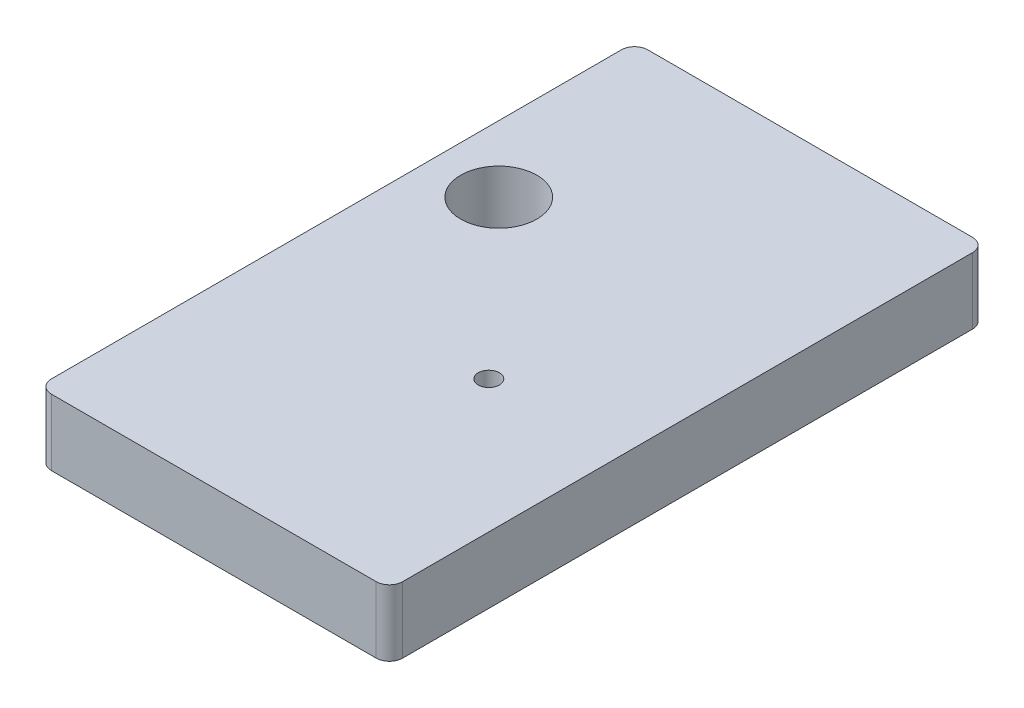
SolidWorks part; units mm, degrees
ref_plane "Plan de face" through (0, 0, 0) normal (0, 0, 1) x (1, 0, 0)
ref_plane "Plan de dessus" through (0, 0, 0) normal (0, 1, 0) x (1, 0, 0)
ref_plane "Plan de droite" through (0, 0, 0) normal (1, 0, 0) x (0, 0, -1)
sketch "Esquisse1" plane through (0, 0, 0) normal (0, 1, 0) x (1, 0, 0)
  line L0 (-6.427, 0) -> (109.1376, 0) construction
  line L1 (0, -7.0221) -> (0, 103.9034) construction
  line L2 (53, -7.0221) -> (53, 103.9034) construction
  line L3 (-6.427, 40) -> (85.7278, 40) construction
  line L4 (-6.427, 90) -> (109.1376, 90) construction
  line L5 (-6.427, 59.5) -> (31.5612, 59.5) construction
  line L6 (0, 88) -> (0, 2)
  line L7 (2, 0) -> (51, 0)
  line L8 (53, 88) -> (53, 2)
  line L9 (10, 81.6582) -> (10, 48.1074) construction
  line L10 (13, 103.9034) -> (13, -7.0221) construction
  line L11 (2, 90) -> (51, 90)
  line L12 (33, 66.665) -> (33, 23.6354) construction
  line L13 (48.8784, 35) -> (28.9431, 35) construction
  arc A0 (51, 90) -> (53, 88) centre (51, 88) cw
  arc A1 (2, 90) -> (0, 88) centre (2, 88) ccw
  arc A2 (51, 0) -> (53, 2) centre (51, 2) ccw
  arc A3 (0, 2) -> (2, 0) centre (2, 2) ccw
  circle A4 centre (10, 59.5) radius 5.75
  circle A5 centre (33, 35) radius 1.6
  point P12 (53, 90)
  point P19 (0, 90)
  point P26 (0, 0)
  dimension "D3" = 2
  dimension "D7" = 10
  dimension "D5" = 2
  dimension "D8" = 5
  dimension "D1" = 90
  dimension "D2" = 40
  dimension "D4" = 50
  dimension "D6" = 19.5
  dimension "D9" = 20
extrude "Extrusion1" add sketch "Esquisse1" along normal blind 10
sketch "Esquisse2" plane through (0, 0, 0) normal (0, -1, 0) x (1, 0, 0)
  line L0 (57.4636, -79) -> (-27.3834, -79) construction
  line L1 (-17.6242, -59.5) -> (57.4636, -59.5) construction
  line L2 (57.4636, -40) -> (-27.3834, -40) construction
  line L3 (57.4636, -20) -> (-27.3834, -20) construction
  line L4 (53, -103.2829) -> (53, 4.7947) construction
  line L5 (57.4636, -10) -> (-27.3834, -10) construction
  line L6 (48, -121.675) -> (48, 4.7947) construction
  line L7 (42, -111.2442) -> (42, 4.7947) construction
  line L8 (57.4636, -90) -> (-27.3834, -90) construction
  line L9 (57.4636, -85) -> (-27.3834, -85) construction
  line L10 (33, -121.675) -> (33, -69.6956) construction
  line L11 (41, -103.2829) -> (41, -69.6956) construction
  line L12 (57.4636, -49.5) -> (28.6431, -49.5) construction
  line L13 (37.3159, -82) -> (19.2671, -82) construction
  line L14 (45, -57.6837) -> (45, -3.061) construction
  line L15 (42, -49.5) -> (49.9748, -57.4748) construction
  line L16 (41, -82.7373) -> (41, -81.2627)
  line L17 (41, -85) -> (33.7489, -77.7489) construction
  line L18 (45.7373, -49.5) -> (44.2627, -49.5)
  line L19 (45.7373, -69.5) -> (44.2627, -69.5)
  line L20 (25, -82.7373) -> (25, -81.2627)
  line L21 (38.7373, -85) -> (27.2627, -85)
  line L22 (38.7373, -79) -> (27.2627, -79)
  line L23 (48, -67.2373) -> (48, -51.7627)
  line L24 (42, -67.2373) -> (42, -51.7627)
  line L25 (24, -67.2373) -> (24, -51.7627)
  line L26 (18, -67.2373) -> (18, -51.7627)
  line L27 (20.2627, -69.5) -> (21.7373, -69.5)
  line L28 (20.2627, -49.5) -> (21.7373, -49.5)
  line L29 (57.4636, -7) -> (6.2084, -7) construction
  line L30 (57.4636, -23) -> (6.2084, -23) construction
  arc A0 (44.2627, -49.5) -> (42, -51.7627) centre (43.1314, -50.6314) ccw
  arc A1 (38.7373, -85) -> (41, -82.7373) centre (39.8686, -83.8686) ccw
  arc A2 (38.7373, -79) -> (41, -81.2627) centre (39.8686, -80.1314) cw
  arc A3 (27.2627, -85) -> (25, -82.7373) centre (26.1314, -83.8686) cw
  arc A4 (27.2627, -79) -> (25, -81.2627) centre (26.1314, -80.1314) ccw
  arc A5 (45.7373, -49.5) -> (48, -51.7627) centre (46.8686, -50.6314) cw
  arc A6 (44.2627, -69.5) -> (42, -67.2373) centre (43.1314, -68.3686) cw
  arc A7 (45.7373, -69.5) -> (48, -67.2373) centre (46.8686, -68.3686) ccw
  arc A8 (20.2627, -69.5) -> (18, -67.2373) centre (19.1314, -68.3686) cw
  arc A9 (21.7373, -69.5) -> (24, -67.2373) centre (22.8686, -68.3686) ccw
  arc A10 (20.2627, -49.5) -> (18, -51.7627) centre (19.1314, -50.6314) ccw
  arc A11 (21.7373, -49.5) -> (24, -51.7627) centre (22.8686, -50.6314) cw
  circle A12 centre (45, -23) radius 1.1
  circle A13 centre (45, -7) radius 1.1
  dimension "D15" = 3
  dimension "D1" = 19.5
  dimension "D2" = 20
  dimension "D3" = 10
  dimension "D4" = 6
  dimension "D5" = 5
  dimension "D6" = 5
  dimension "D7" = 6
  dimension "D8" = 15
  dimension "D9" = 8
  dimension "D10" = 10
  dimension "D11" = 3
  dimension "D12" = 3
  dimension "D13" = 45
  dimension "D14" = 45
  dimension "D16" = 3
extrude "Enlèv. mat.-Extru.1" cut sketch "Esquisse2" against normal blind 4
